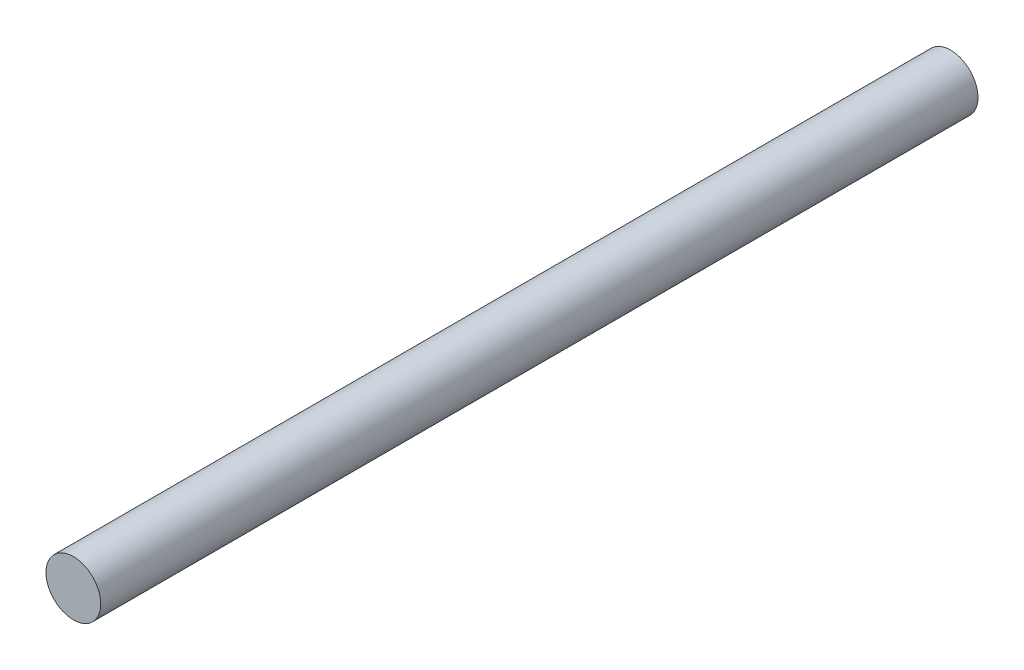
SolidWorks part; units mm, degrees
ref_plane "Front Plane" through (0, 0, 0) normal (0, 0, 1) x (1, 0, 0)
ref_plane "Top Plane" through (0, 0, 0) normal (0, 1, 0) x (1, 0, 0)
ref_plane "Right Plane" through (0, 0, 0) normal (1, 0, 0) x (0, 0, -1)
sketch "Sketch1" plane through (0, 0, 0) normal (0, 0, 1) x (1, 0, 0)
  circle A0 centre (0, 0) radius 2.3813
  dimension "D1" = 4.7625
extrude "Boss-Extrude1" add sketch "Sketch1" along normal blind 76.2
